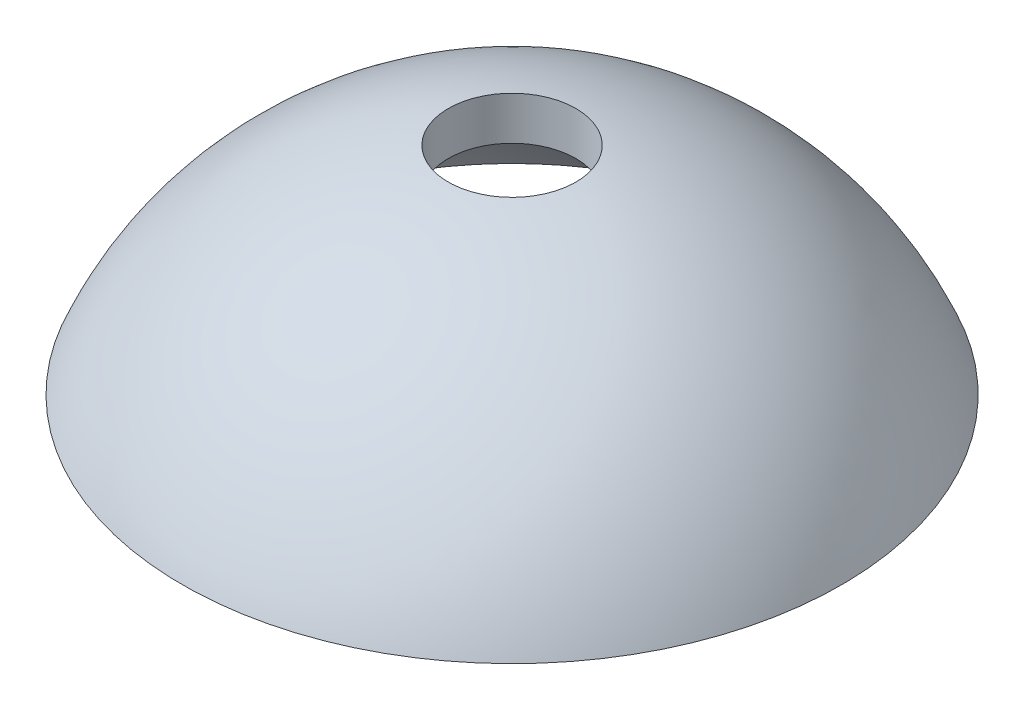
SolidWorks part; units mm, degrees
ref_plane "Front Plane" through (0, 0, 0) normal (0, 0, 1) x (1, 0, 0)
ref_plane "Top Plane" through (0, 0, 0) normal (0, 1, 0) x (1, 0, 0)
ref_plane "Right Plane" through (0, 0, 0) normal (1, 0, 0) x (0, 0, -1)
sketch "Sketch1" plane through (0, 0, 0) normal (1, 0, 0) x (0, 0, -1)
  line L0 (0, 0) -> (0, 50000) construction
  line L1 (0, 6.2747) -> (15.5, 6.31)
  line L2 (3, 16.4641) -> (3, 14.4266)
  line L3 (0, 0) -> (9.747, 11.0509)
  arc A0 (0, 14.7352) -> (13.3181, 6.3051) centre (0, 0) cw
  arc A1 (0, 16.7352) -> (15.5, 6.31) centre (0, 0) cw
  arc A2 (0, 14.7352) -> (13.466, 5.9828) centre (0, 0) cw construction
  arc A3 (0, 16.7352) -> (15.2937, 6.7948) centre (0, 0) cw construction
  point P5 (0, 0)
  point P15 (0, 0)
  point P17 (0, 0)
  point P19 (0, 6.7223)
  point P20 (13.1669, 6.8725)
  point P22 (0, 6.8588)
  point P23 (0, 0)
  point P24 (0, 0)
  point P25 (0, 0)
  point P26 (0, 0)
  point P27 (15.5, 6.3051)
  dimension "D2" = 6
  dimension "D3" = 31
  dimension "D1" = 2
revolve "Revolve1" add sketch "Sketch1" angle 360 about L0
